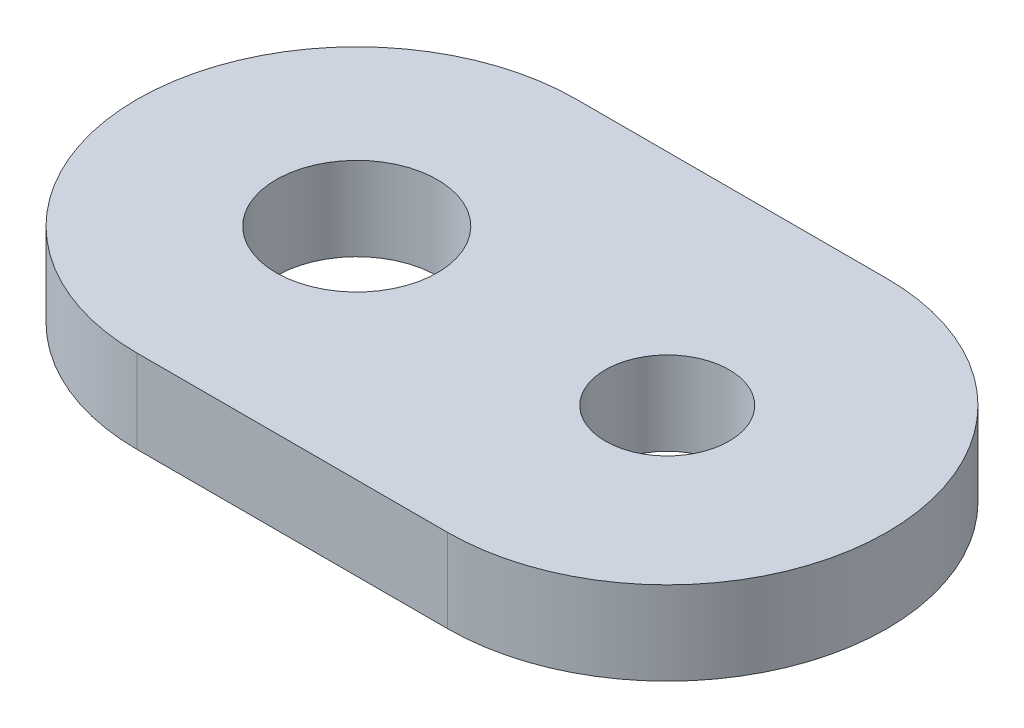
SolidWorks part; units mm, degrees
material "POM ( delrin)"
ref_plane "Front Plane" through (0, 0, 0) normal (0, 0, 1) x (1, 0, 0)
ref_plane "Top Plane" through (0, 0, 0) normal (0, 1, 0) x (1, 0, 0)
ref_plane "Right Plane" through (0, 0, 0) normal (1, 0, 0) x (0, 0, -1)
ref_plane "Plane1" through (0, -3, 0) normal (0, -1, 0) x (1, 0, 0)
sketch "Sketch1" plane through (0, -3, 0) normal (0, -1, 0) x (1, 0, 0)
  line L0 (5.5811, 7.9) -> (-5.5811, 7.9)
  line L1 (-5.5811, -7.9) -> (5.5811, -7.9)
  arc A0 (-5.5811, 7.9) -> (-5.5811, -7.9) centre (-5.5811, 0) ccw
  arc A1 (5.5811, -7.9) -> (5.5811, 7.9) centre (5.5811, 0) ccw
  circle A2 centre (-5.5811, 0) radius 2.9
  circle A3 centre (5.5811, 0) radius 2.225
  dimension "D1" = 5.8
  dimension "D2" = 4.45
  dimension "D4" = 7.9
  dimension "D3" = 11.1622
extrude "Boss-Extrude1" add sketch "Sketch1" against normal blind 3
